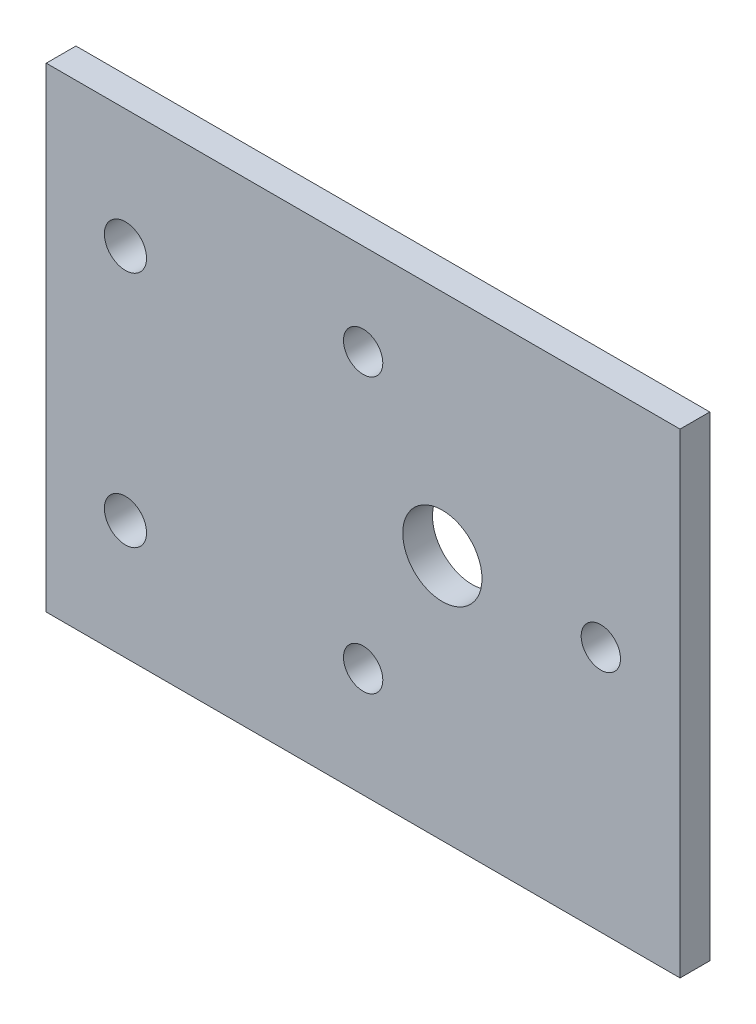
SolidWorks part; units mm, degrees
ref_plane "Front Plane" through (0, 0, 0) normal (0, 0, 1) x (1, 0, 0)
ref_plane "Top Plane" through (0, 0, 0) normal (0, 1, 0) x (1, 0, 0)
ref_plane "Right Plane" through (0, 0, 0) normal (1, 0, 0) x (0, 0, -1)
sketch "Sketch1" plane through (0, 0, 0) normal (0, 0, 1) x (1, 0, 0)
  line L0 (0, 0) -> (101.6, 0)
  line L1 (101.6, 0) -> (101.6, 76.2)
  line L2 (101.6, 76.2) -> (0, 76.2)
  line L4 (0, 76.2) -> (0, 0)
  dimension "D1" = 101.6
  dimension "D2" = 76.2
  dimension "D3" = 101.6
  dimension "D4" = 76.2
extrude "Boss-Extrude1" add sketch "Sketch1" along normal blind 4.7625
sketch "Sketch2" plane through (0, 0, 4.7625) normal (0, 0, 1) x (1, 0, 0)
  line L0 (101.6, 76.2) -> (0, 76.2) construction
  line L1 (0, 0) -> (101.6, 0) construction
  line L2 (0, 76.2) -> (0, 0) construction
  circle A0 centre (12.7, 57.15) radius 3.3782
  circle A1 centre (12.7, 19.05) radius 3.3782
  dimension "D1" = 6.7564
  dimension "D2" = 6.7564
  dimension "D3" = 19.05
  dimension "D4" = 19.05
  dimension "D5" = 12.7
  dimension "D6" = 12.7
extrude "Cut-Extrude1" cut sketch "Sketch2" against normal through all
sketch "Sketch3" plane through (0, 0, 4.7625) normal (0, 0, 1) x (1, 0, 0)
  line L0 (101.6, 0) -> (101.6, 76.2) construction
  circle A0 centre (63.5, 39.5469) radius 6.35
  circle A1 centre (50.8, 61.5439) radius 3.15
  circle A2 centre (88.9, 39.5469) radius 3.15
  circle A3 centre (50.8, 17.5498) radius 3.15
  point P12 (63.5, 39.5469)
  dimension "D1" = 12.7
  dimension "D2" = 38.1
  dimension "D3" = 6.3
  dimension "D5" = 25.4
  dimension "D6" = 25.4
  dimension "D7" = 25.4
  dimension "D4" = 3
extrude "Cut-Extrude2" cut sketch "Sketch3" against normal through all
